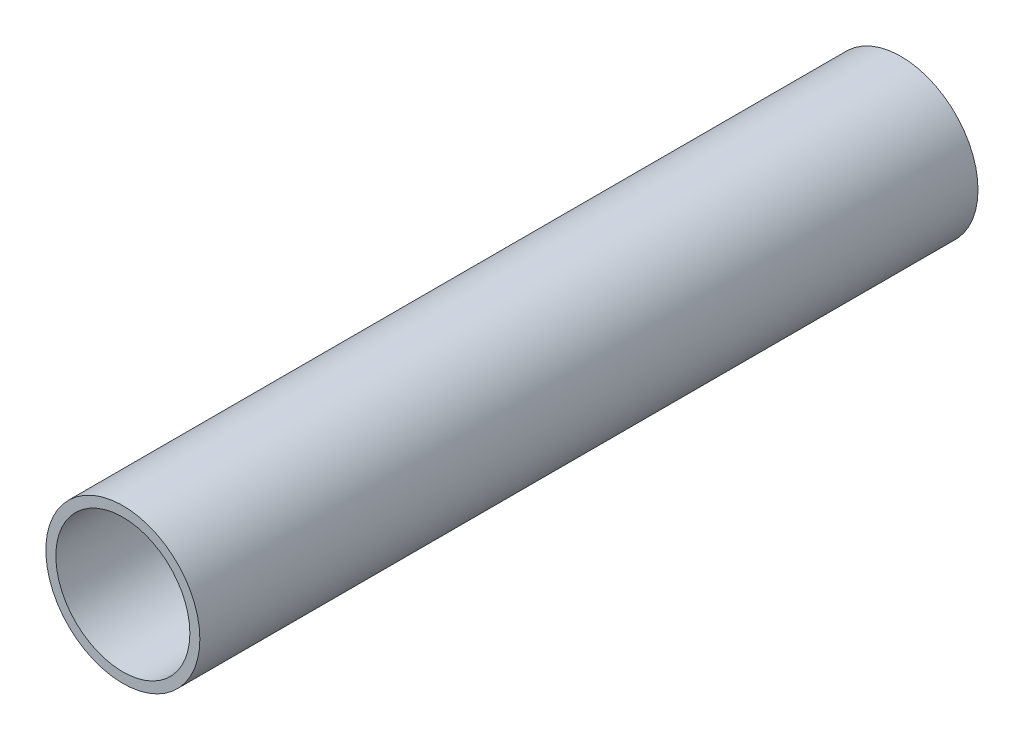
SolidWorks part; units mm, degrees
ref_plane "Front Plane" through (0, 0, 0) normal (0, 0, 1) x (1, 0, 0)
ref_plane "Top Plane" through (0, 0, 0) normal (0, 1, 0) x (1, 0, 0)
ref_plane "Right Plane" through (0, 0, 0) normal (1, 0, 0) x (0, 0, -1)
sketch "Sketch1" plane through (0, 0, 0) normal (0, 0, 1) x (1, 0, 0)
  circle A0 centre (0, 0) radius 30.1625
  circle A1 centre (0, 0) radius 26.2509
  dimension "D1" = 60.325
  dimension "D2" = 52.5018
extrude "Boss-Extrude1" add sketch "Sketch1" along normal blind 304.8 contours A0 | A1
